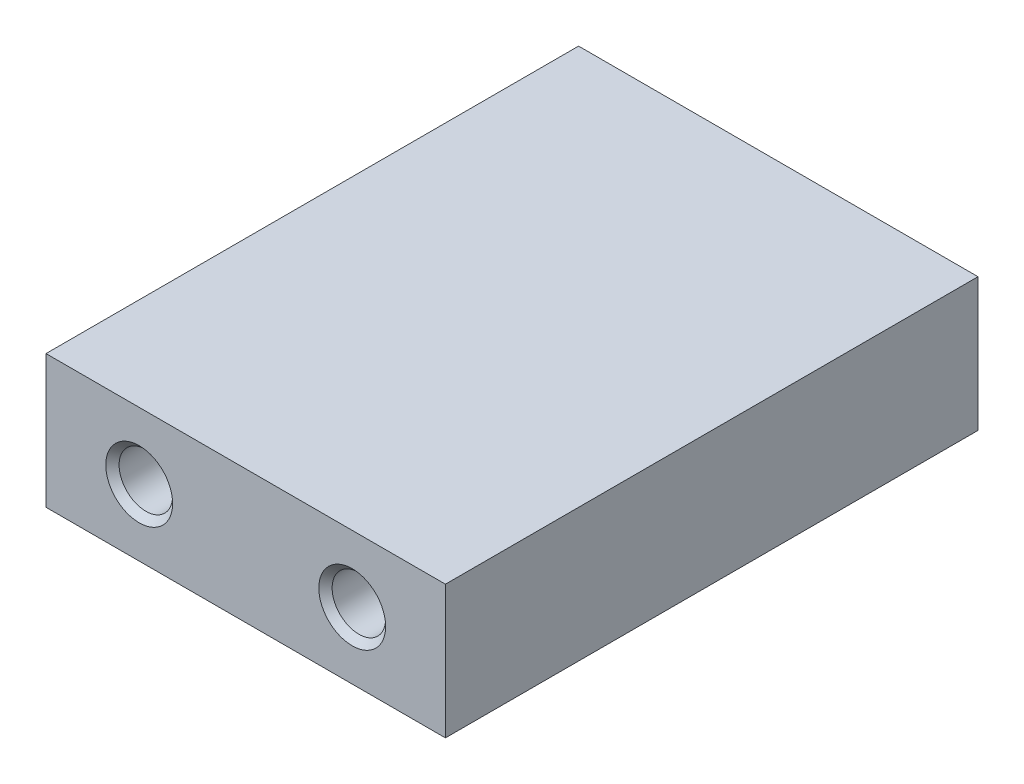
SolidWorks part; units mm, degrees
material "6063-T5"
ref_plane "Front Plane" through (0, 0, 0) normal (0, 0, 1) x (1, 0, 0)
ref_plane "Top Plane" through (0, 0, 0) normal (0, 1, 0) x (1, 0, 0)
ref_plane "Right Plane" through (0, 0, 0) normal (1, 0, 0) x (0, 0, -1)
sketch "Sketch1" plane through (0, 0, 0) normal (0, 0, 1) x (1, 0, 0)
  line L1 (-19.05, -6.35) -> (19.05, -6.35)
  line L2 (-19.05, -6.35) -> (-19.05, 6.35)
  line L3 (-19.05, 6.35) -> (19.05, 6.35)
  line L4 (19.05, -6.35) -> (19.05, 6.35)
  line L5 (-19.05, -6.35) -> (19.05, 6.35) construction
  line L6 (-19.05, 6.35) -> (19.05, -6.35) construction
  point P0 (0, 0)
  dimension "D1" = 38.1
  dimension "D2" = 12.7
extrude "Boss-Extrude1" add sketch "Sketch1" against normal blind 50.8
sketch "Sketch2" plane through (0, 0, 0) normal (0, 0, 1) x (1, 0, 0)
  line L1 (0, -1000) -> (0, 49000) construction
  point P0 (-10.16, 0)
  point P1 (10.16, 0)
  dimension "D1" = 20.32
hole_wizard "1/4-20 Tapped Hole1" positions "3DSketch1" profile "Sketch4" tap size "1/4-20" standard "ANSI Inch"
sketch3d "3DSketch1"
  point P0 (-10.16, 0, 0)
  point P3 (10.16, 0, 0)
sketch "Sketch4" plane through (-10.16, 0, 0) normal (1, 0, 0) x (0, -1, 0)
  line L0 (0, 0) -> (0, 14.2338)
  line L1 (0, 14.2338) -> (2.5527, 12.7)
  line L2 (2.5527, 12.7) -> (2.5527, 0.635)
  line L3 (2.5527, 0.635) -> (3.1877, 0)
  line L5 (3.1877, 0) -> (0, 0)
  line L6 (-2.5527, 0.635) -> (-3.1877, 0) construction
  line L10 (0, 14.2338) -> (-2.5527, 12.7) construction
  line L11 (0, -6.35) -> (0, 107.95) construction
  dimension "Tap Drill Dia." = 5.1054
  dimension "Tap Drill Depth" = 12.7
  dimension "Near C'Sink Dia." = 6.3754
  dimension "Near C'Sink Angle" = 90
  dimension "Drill Angle" = 118
cosmetic thread "Hole Thread1" parameters "D1"=10.16, "D2"=6.35
cosmetic thread "Hole Thread2" parameters "D1"=10.16, "D2"=6.35
ref_plane "Plane1" through (0, 0, -25.4) normal (0, 0, 1) x (1, 0, 0)
mirror "Mirror1" about plane through (0, 0, -25.4) normal (0, 0, 1) of "1/4-20 Tapped Hole1"
sketch "Sketch5" plane through (0, 6.35, 0) normal (0, 1, 0) x (1, 0, 0)
  line L0 (0, -1000) -> (0, 49000) construction
  line L1 (-999.1252, 25.4) -> (49000.8748, 25.4) construction
  line L3 (19.05, 0) -> (-19.05, 0) construction
  line L4 (19.05, 50.8) -> (-19.05, 50.8) construction
  point P4 (0, 38.1)
  point P6 (0, 12.7)
  dimension "D1" = 25.4
sketch "Sketch11" plane through (-19.05, 0, 0) normal (-1, 0, 0) x (0, 0, 1)
  line L0 (-1048.0986, 0) -> (48951.9014, 0) construction
  line L1 (-25.4, -1002.8477) -> (-25.4, 48997.1523) construction
  line L2 (-25.4, -6.985) -> (-25.4, 6.985) construction
  line L3 (201000, 6.35) -> (-249000, 6.35) construction
  line L4 (-50.8, -6.35) -> (0, -6.35) construction
  point P10 (-34.29, 0)
  point P11 (-16.51, 0)
  dimension "D1" = 17.78
hole_wizard "1/8 (0.125) Diameter Hole1" positions "Sketch12" profile "Sketch13" hole size "1/8" standard "ANSI Inch"
sketch "Sketch12" plane through (-19.05, 0, 0) normal (-1, 0, 0) x (0, 0, 1)
  point P0 (-34.29, 0)
  point P3 (-16.51, 0)
sketch "Sketch13" plane through (-19.05, 0, -34.29) normal (0, 1, 0) x (0, 0, 1)
  line L0 (0, 0) -> (0, 6.0339)
  line L1 (0, 6.0339) -> (1.5875, 5.08)
  line L2 (1.5875, 5.08) -> (1.5875, 0)
  line L5 (1.5875, 0) -> (0, 0)
  line L10 (0, 6.0339) -> (-1.5875, 5.08) construction
  line L11 (0, -6.35) -> (0, 107.95) construction
  dimension "Hole Dia." = 3.175
  dimension "Hole Depth" = 5.08
  dimension "Drill Angle" = 118
